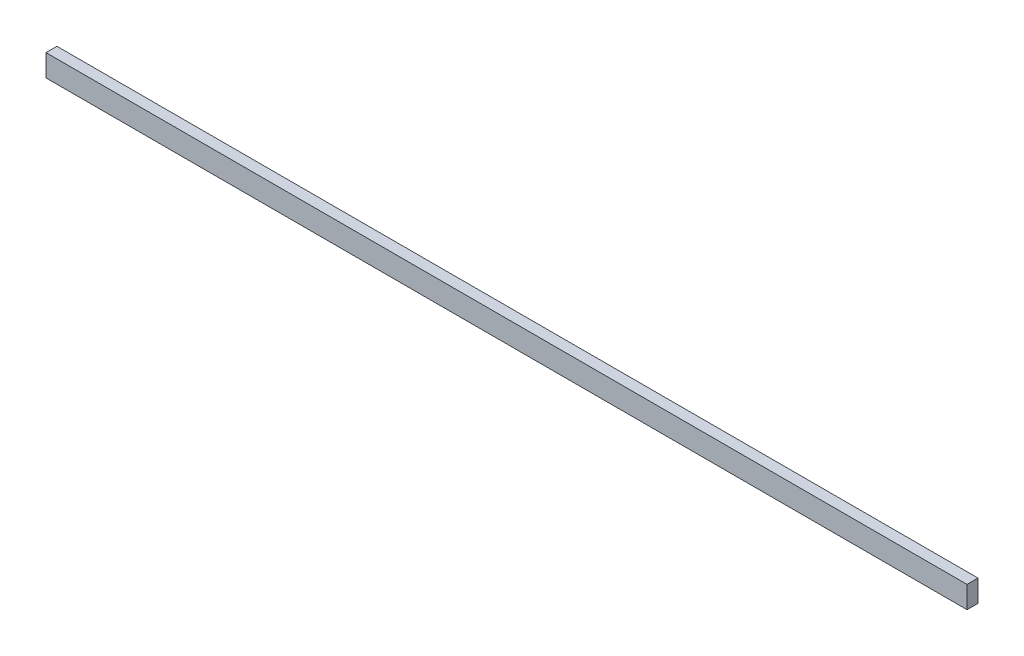
SolidWorks part; units mm, degrees
ref_plane "Front Plane" through (0, 0, 0) normal (0, 0, 1) x (1, 0, 0)
ref_plane "Top Plane" through (0, 0, 0) normal (0, 1, 0) x (1, 0, 0)
ref_plane "Right Plane" through (0, 0, 0) normal (1, 0, 0) x (0, 0, -1)
sketch "Sketch1" plane through (0, 0, 0) normal (0, 1, 0) x (1, 0, 0)
  line L1 (0, 0) -> (2133.6, 0)
  line L2 (0, 0) -> (0, 25.4)
  line L3 (0, 25.4) -> (2133.6, 25.4)
  line L4 (2133.6, 0) -> (2133.6, 25.4)
  dimension "D1" = 2133.6
  dimension "D2" = 25.4
extrude "Boss-Extrude1" add sketch "Sketch1" along normal blind 50.8
